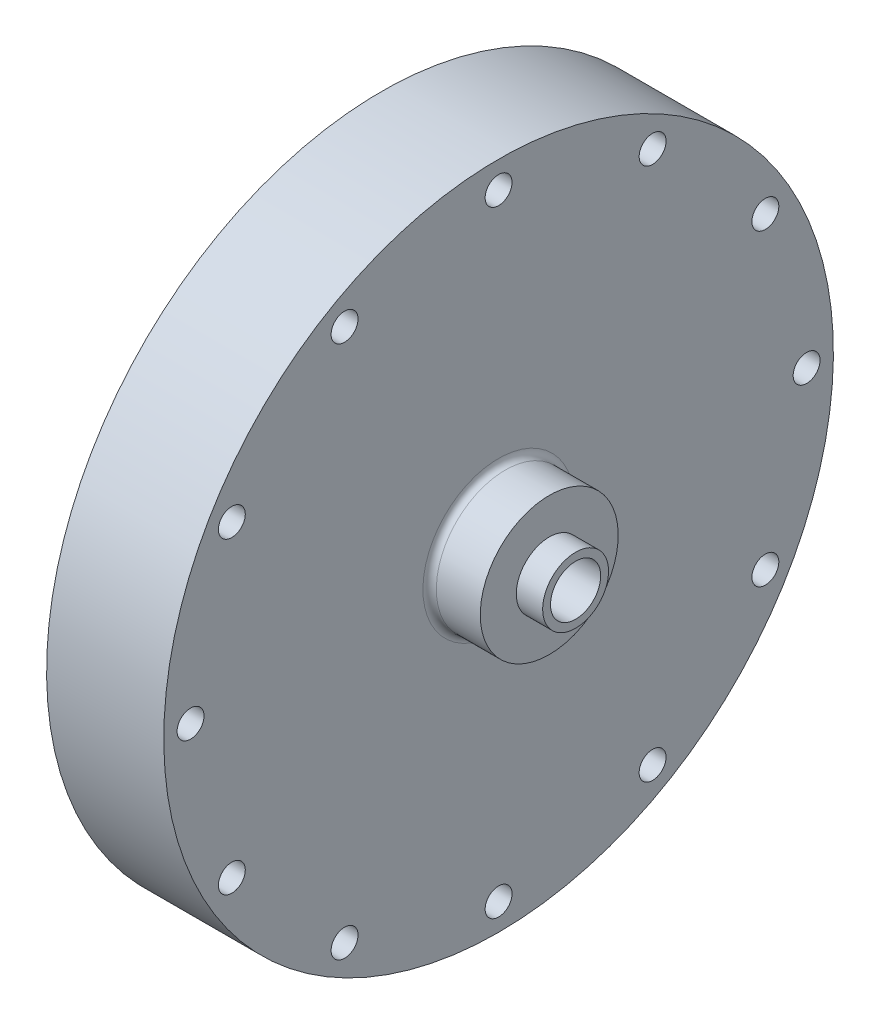
SolidWorks part; units mm, degrees
material "7075-T6 (SN)"
ref_plane "Front Plane" through (0, 0, 0) normal (0, 0, 1) x (1, 0, 0)
ref_plane "Top Plane" through (0, 0, 0) normal (0, 1, 0) x (1, 0, 0)
ref_plane "Right Plane" through (0, 0, 0) normal (1, 0, 0) x (0, 0, -1)
sketch "Sketch2" plane through (0, 0, 0) normal (0, 0, 1) x (1, 0, 0)
  line L0 (9.525, 0) -> (165.0115, 0) construction
  line L5 (41.355, 13.081) -> (41.355, 6.2484)
  line L6 (31.75, 13.081) -> (41.355, 13.081)
  line L7 (41.355, 6.2484) -> (46.355, 6.2484)
  line L8 (46.355, 6.2484) -> (46.355, 0)
  line L9 (9.525, 0) -> (46.355, 0)
  line L16 (9.525, 0) -> (9.525, 63.5)
  line L18 (31.75, 63.5) -> (31.75, 13.081)
  line L19 (31.75, 63.5) -> (9.525, 63.5)
  dimension "D1" = 63.5
  dimension "D2" = 36.83
  dimension "D4" = 13.081
  dimension "D5" = 22.225
  dimension "D7" = 6.2484
  dimension "D8" = 5
revolve "Main Structure" add sketch "Sketch2" angle 360 about L0
cosmetic thread "Cosmetic Thread1" parameters "D2"=23.1953
sketch "Sketch3" plane through (46.355, 0, 0) normal (1, 0, 0) x (0, 0, -1)
  circle A0 centre (0, 0) radius 4.7625
  dimension "D1" = 9.525
extrude "Oxidizer Inlet Hole" cut sketch "Sketch3" against normal through all
sketch "Sketch4" plane through (31.75, 0, 0) normal (-1, 0, 0) x (0, 0, 1)
  circle A0 centre (0, 0) radius 58.42 construction
  circle A1 centre (0, -58.42) radius 2.146
  circle A2 centre (-29.21, -50.5932) radius 2.146
  circle A3 centre (-50.5932, -29.21) radius 2.146
  circle A4 centre (-58.42, 0) radius 2.146
  circle A5 centre (-50.5932, 29.21) radius 2.146
  circle A6 centre (-29.21, 50.5932) radius 2.146
  circle A7 centre (0, 58.42) radius 2.146
  circle A8 centre (29.21, 50.5932) radius 2.146
  circle A9 centre (50.5932, 29.21) radius 2.146
  circle A10 centre (58.42, 0) radius 2.146
  circle A11 centre (50.5932, -29.21) radius 2.146
  circle A12 centre (29.21, -50.5932) radius 2.146
  point P29 (0, 0)
  dimension "D1" = 12
  dimension "D2" = 116.84
hole_wizard "Flange Holes" positions "Sketch7" profile "Sketch8" hole size "#7" standard "ANSI Inch" end condition up to next
sketch "Sketch7" plane through (31.75, 0, 0) normal (-1, 0, 0) x (0, 0, 1)
  point P0 (0, -58.42)
  point P3 (-29.21, -50.5932)
  point P6 (-50.5932, -29.21)
  point P9 (-58.42, 0)
  point P12 (-50.5932, 29.21)
  point P15 (-29.21, 50.5932)
  point P18 (0, 58.42)
  point P21 (29.21, 50.5932)
  point P24 (50.5932, 29.21)
  point P27 (58.42, 0)
  point P30 (50.5932, -29.21)
  point P33 (29.21, -50.5932)
sketch "Sketch8" plane through (31.75, -58.42, 0) normal (0, 1, 0) x (0, 0, -1)
  line L0 (0, 0) -> (0, 22.225)
  line L1 (0, 22.225) -> (2.5527, 22.225)
  line L2 (2.5527, 22.225) -> (2.5527, 0)
  line L5 (2.5527, 0) -> (0, 0)
  line L11 (0, -6.35) -> (0, 107.95) construction
  dimension "Thru Hole Dia." = 5.1054
  dimension "Thru Hole Depth" = 22.225
sketch "Sketch9" plane through (9.525, 0, 0) normal (-1, 0, 0) x (0, 0, 1)
  line L0 (0, 0) -> (-67.6727, 18.1329) construction
  line L1 (0, 0) -> (-58.42, 0) construction
  circle A0 centre (0, 0) radius 58.42 construction
  circle A1 centre (-56.4294, 15.1202) radius 2.9451
  circle A2 centre (56.4294, -15.1202) radius 2.9451
  point P14 (0, 0)
  dimension "D1" = 15
  dimension "D2" = 2
hole_wizard "Dowel Holes" positions "Sketch10" profile "Sketch11" hole size "3/16" standard "ANSI Inch"
sketch "Sketch10" plane through (9.525, 0, 0) normal (-1, 0, 0) x (0, 0, 1)
  point P0 (56.4294, -15.1202)
  point P3 (-56.4294, 15.1202)
sketch "Sketch11" plane through (9.525, -15.1202, 56.4294) normal (0, 1, 0) x (0, 0, 1)
  line L0 (0, 0) -> (0, 7.7808)
  line L1 (0, 7.7808) -> (2.3812, 6.35)
  line L2 (2.3812, 6.35) -> (2.3812, 0)
  line L5 (2.3812, 0) -> (0, 0)
  line L10 (0, 7.7808) -> (-2.3812, 6.35) construction
  line L11 (0, -6.35) -> (0, 107.95) construction
  dimension "Hole Dia." = 4.7625
  dimension "Hole Depth" = 6.35
  dimension "Drill Angle" = 118
sketch "Sketch12" plane through (9.525, 0, 0) normal (-1, 0, 0) x (0, 0, 1)
  circle A0 centre (0, 0) radius 28.575
  dimension "D1" = 57.15
extrude "Cut-Extrude2" cut sketch "Sketch12" against normal blind 9.525
ref_plane "Plane1" through (9.525, 0, 0) normal (-1, 0, 0) x (0, 0, 1)
ref_plane "Plane4" through (19.05, 0, 0) normal (-1, 0, 0) x (0, 0, 1)
sketch "Sketch16" plane through (19.05, 0, 0) normal (-1, 0, 0) x (0, 0, 1)
  circle A0 centre (0, 0) radius 28.575
  dimension "D1" = 57.15
ref_plane "Plane2" through (30.48, 0, 0) normal (-1, 0, 0) x (0, 0, 1)
sketch "Sketch17" plane through (30.48, 0, 0) normal (-1, 0, 0) x (0, 0, 1)
  circle A0 centre (0, 0) radius 4.7625
  dimension "D1" = 9.525
loft "Internal Flow Path Loft Cut" cut profiles "Sketch16", "Sketch17"
sketch "Sketch18" plane through (9.525, 0, 0) normal (-1, 0, 0) x (0, 0, 1)
  circle A0 centre (0, 0) radius 33.3375
  circle A1 centre (33.3375, 0) radius 1.5042
  dimension "D1" = 66.675
hole_wizard "#4-40 Tapped Hole1" positions "Sketch19" profile "Sketch20" tap size "#4-40" standard "ANSI Inch"
sketch "Sketch19" plane through (9.525, 0, 0) normal (-1, 0, 0) x (0, 0, 1)
  point P0 (33.3375, 0)
sketch "Sketch20" plane through (9.525, 0, 33.3375) normal (0, 1, 0) x (0, 0, 1)
  line L0 (0, 0) -> (0, 13.8872)
  line L1 (0, 13.8872) -> (1.1303, 13.208)
  line L2 (1.1303, 13.208) -> (1.1303, 0)
  line L5 (1.1303, 0) -> (0, 0)
  line L10 (0, 13.8872) -> (-1.1303, 13.208) construction
  line L11 (0, -6.35) -> (0, 107.95) construction
  dimension "Tap Drill Dia." = 2.2606
  dimension "Tap Drill Depth" = 13.208
  dimension "Drill Angle" = 118
cosmetic thread "Hole Thread1" parameters "D1"=9.398, "D2"=2.8448
pattern_circular "CirPattern1" count 8 over 360 about axis through (0, 0, 0) along (1, 0, 0) of "#4-40 Tapped Hole1"
fillet "Fillet1" radius 1.27 1 edges at (31.75, -13.081, 0)
